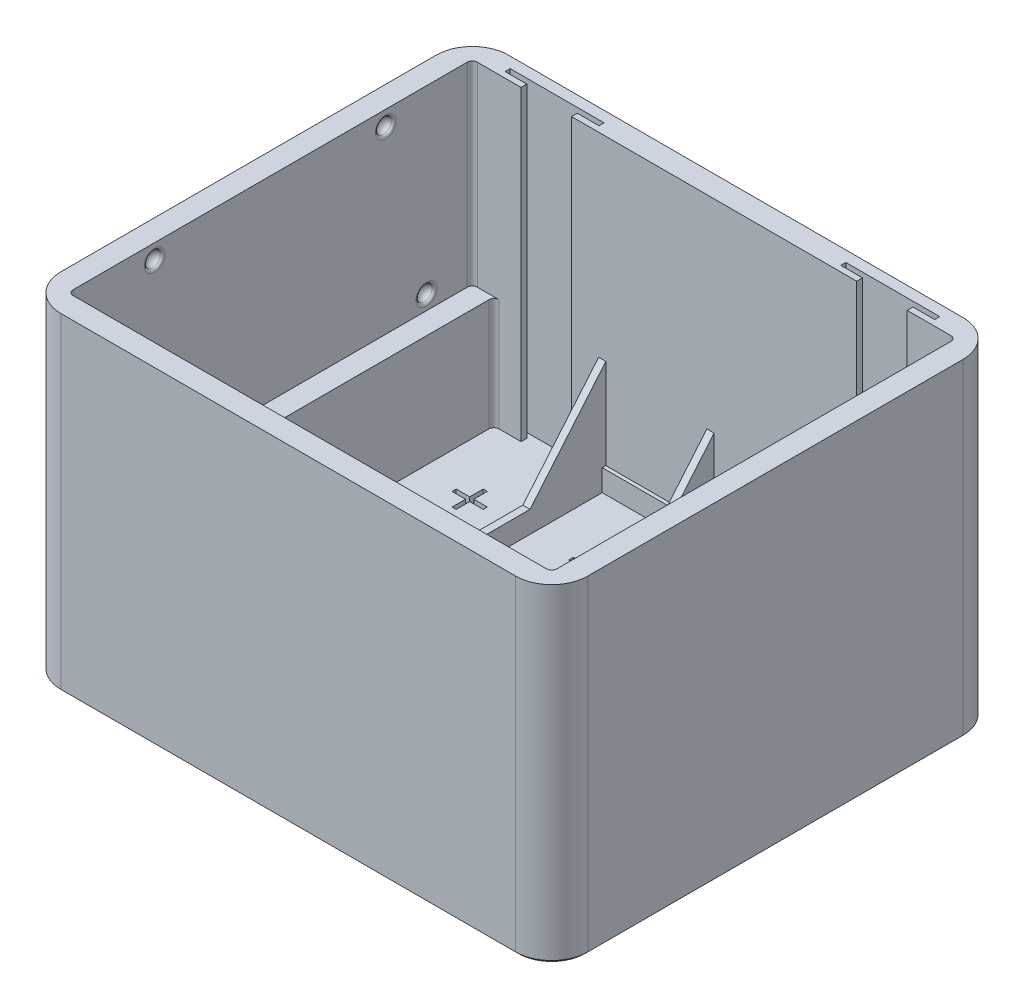
SolidWorks part; units mm, degrees
ref_plane "Front Plane" through (0, 0, 0) normal (0, 0, 1) x (1, 0, 0)
ref_plane "Top Plane" through (0, 0, 0) normal (0, 1, 0) x (1, 0, 0)
ref_plane "Right Plane" through (0, 0, 0) normal (1, 0, 0) x (0, 0, -1)
sketch "Sketch1" plane through (0, 0, 0) normal (0, 1, 0) x (1, 0, 0)
  line L1 (-33.5, -31) -> (33.5, -31)
  line L2 (-33.5, -31) -> (-33.5, 31)
  line L3 (-33.5, 31) -> (33.5, 31)
  line L4 (33.5, -31) -> (33.5, 31)
  line L5 (-33.5, -31) -> (33.5, 31) construction
  line L6 (-33.5, 31) -> (33.5, -31) construction
  point P0 (0, 0)
  dimension "D1" = 62
  dimension "D2" = 67
extrude "Boss-Extrude1" add sketch "Sketch1" along normal blind 3
sketch "Sketch2" plane through (0, 3, 0) normal (0, 1, 0) x (1, 0, 0)
  line L0 (-30.5, -28) -> (-30.5, 28)
  line L1 (-33.5, -31) -> (33.5, -31)
  line L2 (-33.5, -31) -> (-33.5, 31)
  line L3 (-33.5, 31) -> (33.5, 31)
  line L4 (33.5, -31) -> (33.5, 31)
  line L5 (-33.5, -31) -> (33.5, 31) construction
  line L6 (-33.5, 31) -> (33.5, -31) construction
  line L7 (-30.5, 28) -> (30.5, 28)
  line L8 (30.5, -28) -> (30.5, 28)
  line L9 (-30.5, -28) -> (30.5, -28)
  line L11 (-16, 28) -> (-15, 28)
  line L12 (-16, 28) -> (-16, -28)
  line L13 (-16, -28) -> (-15, -28)
  line L14 (-15, 28) -> (-15, -28)
  line L15 (-0.5, 28) -> (0.5, 28)
  line L16 (-0.5, 28) -> (-0.5, -28)
  line L17 (-0.5, -28) -> (0.5, -28)
  line L18 (0.5, 28) -> (0.5, -28)
  line L19 (15, 28) -> (16, 28)
  line L20 (15, 28) -> (15, -28)
  line L21 (15, -28) -> (16, -28)
  line L22 (16, 28) -> (16, -28)
  point P0 (0, 0)
  point P29 (0, 28)
  line M9 (33.5, -31) -> (33.5, 31)
  line M10 (33.5, 31) -> (-33.5, 31)
  line M11 (-33.5, 31) -> (-33.5, -31)
  line M12 (-33.5, -31) -> (33.5, -31)
  dimension "D2" = 14.5
  dimension "D3" = 14.5
  dimension "D4" = 14.5
  dimension "D1" = 3
extrude "Boss-Extrude2" add sketch "Sketch2" along normal blind 15.5 contours L9 L0 L7 L8 M12 M9 M10 M11 | L14 L7 L12 L9 | L18 L17 L16 L15 | L20 L21 L22 L19
sketch "Sketch4" plane through (-16, 0, 0) normal (-1, 0, 0) x (0, 0, 1)
  line L0 (-28, 18.5) -> (-17.5, 6)
  line L1 (-31, 18.5) -> (31, 18.5) construction
  line L2 (-17.5, 6) -> (17.5, 6)
  line L3 (17.5, 6) -> (28, 18.5)
  line L5 (-28, 3) -> (28, 3) construction
  line L6 (-28, 18.5) -> (28, 18.5)
  point P4 (0, 6)
  dimension "D1" = 35
  dimension "D2" = 3
extrude "Cut-Extrude1" cut sketch "Sketch4" against normal up to surface (32 mm away) up to face at (16, 10.75, 0)
sketch "Sketch5" plane through (-33.5, 0, 0) normal (-1, 0, 0) x (0, 0, 1)
  line L1 (-31, 18.5) -> (31, 18.5)
  line L2 (-31, 18.5) -> (-31, 0)
  line L3 (-31, 0) -> (31, 0)
  line L4 (31, 18.5) -> (31, 0)
extrude "Boss-Extrude4" add sketch "Sketch5" along normal blind 3
sketch "Sketch17" plane through (33.5, 0, 0) normal (1, 0, 0) x (0, 0, -1)
  line L1 (-31, 18.5) -> (31, 18.5)
  line L2 (-31, 18.5) -> (-31, 0)
  line L3 (-31, 0) -> (31, 0)
  line L4 (31, 18.5) -> (31, 0)
extrude "Boss-Extrude7" add sketch "Sketch17" along normal blind 3
sketch "Sketch7" plane through (0, 18.5, 0) normal (0, 1, 0) x (1, 0, 0)
  line L1 (-36.5, -31) -> (36.5, -31) construction
  line L3 (36.5, 31) -> (-36.5, 31) construction
  line L5 (-36.5, -31) -> (36.5, -31)
  line L6 (36.5, -31) -> (36.5, 31)
  line L7 (36.5, 31) -> (-36.5, 31)
  line L9 (33.5, 28) -> (-33.5, 28)
  line L10 (33.5, -28) -> (33.5, 28)
  line L11 (-33.5, -28) -> (33.5, -28)
  line L12 (-36.5, -31) -> (-36.5, 31)
  line L17 (-36.5, -31) -> (-36.5, 31) construction
  line L18 (-33.5, -28) -> (-33.5, 28)
  line L19 (-33.5, -28) -> (-33.5, 28) construction
  dimension "D1" = 3
extrude "Boss-Extrude5" add sketch "Sketch7" along normal blind 27
sketch "Sketch10" plane through (0, 3, 0) normal (0, 1, 0) x (1, 0, 0)
  text T0 "+" font "Century Gothic" height in points 24
  text T1 "-" font "Century Gothic" height in points 24
  text T2 "-" font "Century Gothic" height in points 24
  text T3 "+" font "Century Gothic" height in points 24
  text T4 "+" font "Century Gothic" height in points 24
  text T5 "-" font "Century Gothic" height in points 24
  text T6 "-" font "Century Gothic" height in points 24
  text T7 "+" font "Century Gothic" height in points 24
extrude "Cut-Extrude4" cut sketch "Sketch10" against normal blind 1
sketch "Sketch11" plane through (0, 18.5, 0) normal (0, 1, 0) x (1, 0, 0)
  line L1 (-16, -28) -> (-15, -28)
  line L2 (-16, -28) -> (-16, -27.5)
  line L3 (-16, -27.5) -> (-15, -27.5)
  line L4 (-15, -28) -> (-15, -27.5)
  line L5 (0.5, 28) -> (-0.5, 28)
  line L6 (0.5, 28) -> (0.5, 27.5)
  line L7 (0.5, 27.5) -> (-0.5, 27.5)
  line L8 (-0.5, 28) -> (-0.5, 27.5)
  line L9 (15, -27.5) -> (16, -27.5)
  line L10 (15, -27.5) -> (15, -28)
  line L11 (15, -28) -> (16, -28)
  line L12 (16, -27.5) -> (16, -28)
  line L14 (-15, -28) -> (-16, -28) construction
  line L15 (-16, 28) -> (-16, -28) construction
  line L16 (0.5, 28) -> (-0.5, 28) construction
  line L17 (-0.5, 17.5) -> (-0.5, 28) construction
  line L18 (16, -28) -> (15, -28) construction
  line L19 (15, -28) -> (15, -17.5) construction
  line L20 (-29.75, 28.8) -> (-26.75, 28.8)
  line L21 (-26.75, 28.8) -> (-26.75, 28)
  line L22 (-33.5, 28) -> (33.5, 28) construction
  line L23 (-26.75, 28) -> (-19.75, 28)
  line L24 (-19.75, 28) -> (-19.75, 28.8)
  line L25 (-19.75, 28.8) -> (-16.75, 28.8)
  line L26 (-16.75, 28.8) -> (-16.75, 29.5)
  line L27 (-16.75, 29.5) -> (-29.75, 29.5)
  line L28 (-29.75, 29.5) -> (-29.75, 28.8)
  line L29 (16.75, 28.8) -> (16.75, 29.5)
  line L30 (16.75, 29.5) -> (29.75, 29.5)
  line L31 (29.75, 29.5) -> (29.75, 28.8)
  line L32 (29.75, 28.8) -> (26.75, 28.8)
  line L33 (26.75, 28.8) -> (26.75, 28)
  line L34 (16, 28) -> (30.5, 28) construction
  line L35 (26.75, 28) -> (19.75, 28)
  line L36 (19.75, 28) -> (19.75, 28.8)
  line L37 (19.75, 28.8) -> (16.75, 28.8)
  line L38 (-30.5, 28) -> (-16, 28) construction
  line L39 (16, 28) -> (30.5, 28) construction
  point P15 (0, 28)
  point P17 (0, 28)
  point P21 (-15.5, -28)
  point P22 (-15.5, -28)
  point P30 (15.5, -28)
  point P31 (15.5, -28)
  point P42 (23.25, 28)
  point P51 (-23.25, 28)
  point P56 (-23.25, 28)
  point P57 (23.25, 28)
  dimension "D1" = 0.5
  dimension "D2" = 0.7
  dimension "D3" = 0.8
  dimension "D4" = 13
  dimension "D5" = 7
extrude "Cut-Extrude5" cut sketch "Sketch11" against normal up to surface (15.5 mm away) and the other way through all up to face at (-23.3935, 3, -17.5339)
fillet "Fillet1" radius 5 4 edges at (36.5, 22.75, 31) (-36.5, 22.75, 31) (-36.5, 22.75, -31) (36.5, 22.75, -31)
fillet "Fillet2" radius 0.7 8 edges at (30.5, 10.75, 28) (30.5, 10.75, -28) (-33.5, 32, -28) (-30.5, 10.75, -28) (-30.5, 10.75, 28) (-33.5, 32, 28) (33.5, 32, 28) (33.5, 32, -28)
chamfer "Chamfer2" distance 0.4 angle 45 8 edges at (0, 0, -31) (-35.0355, 0, -29.5355) (-36.5, 0, 0) (-35.0355, 0, 29.5355) (0, 0, 31) (35.0355, 0, -29.5355) (36.5, 0, 0) (35.0355, 0, 29.5355)
sketch "Sketch15" [suppressed] plane through (0, 0, -28) normal (0, 0, 1) x (1, 0, 0)
  line L0 (-15, 3) -> (-0.5, 3) construction
  line L2 (15, 3) -> (0.5, 3) construction
  line L3 (0.5, 3) -> (0.5, 17.9048) construction
  line L4 (0.5, 3) -> (0.5, 17.9048)
  line L5 (-0.5, 3) -> (-0.5, 17.9048) construction
  line L6 (-0.5, 3) -> (-0.5, 17.9048)
  line L7 (-7.75, 9.6425) -> (7.75, 9.6425)
  point P8 (-7.75, 3)
  point P10 (7.75, 3)
sketch "Sketch16" plane through (0, 3, 0) normal (0, 1, 0) x (1, 0, 0)
  line L6 (-15, 17.5) -> (-15, 28) construction
  line L7 (15, 28) -> (-15, 28)
  line L8 (15, 28) -> (15, 27.5)
  line L9 (15, 27.5) -> (-15, 27.5)
  line L10 (-15, 28) -> (-15, 27.5)
  line L11 (0.5, 27.5) -> (-0.5, 27.5) construction
extrude "Boss-Extrude6" add sketch "Sketch16" along normal blind 3
ref_plane "Plane1" through (0, 20.5, 0) normal (0, 1, 0) x (1, 0, 0)
sketch "Sketch19" plane through (0, 20.5, 0) normal (0, 1, 0) x (1, 0, 0)
  line L0 (33.5, -27.3) -> (33.5, 27.3) construction
  line L1 (33.5, -27.3) -> (33.5, 27.3) construction
  line L2 (33.5, -20.55) -> (33.5, -21.65)
  line L3 (33.5, -21.65) -> (34.6, -21.65)
  line L4 (29.8, -28) -> (32.8, -28) construction
  arc A0 (33.5, -20.55) -> (34.6, -21.65) centre (33.5, -21.65) cw
  dimension "D1" = 1.1
  dimension "D2" = 6.35
revolve "Cut-Revolve1" cut sketch "Sketch19" angle 360 about L3
mirror "Mirror1" about plane through (0, 0, 0) normal (0, 0, 1) of "Cut-Revolve1"
mirror "Mirror2" about plane through (0, 0, 0) normal (1, 0, 0) of "Mirror1", "Cut-Revolve1"
fillet "Fillet3" radius 0.4 4 edges at (33.5, 20.5, 22.75) (33.5, 20.5, -22.75) (-33.5, 20.5, 22.75) (-33.5, 20.5, -22.75)
ref_plane "Plane2" through (0, 43.4, 0) normal (0, 1, 0) x (1, 0, 0)
sketch "Sketch20" plane through (0, 43.4, 0) normal (0, 1, 0) x (1, 0, 0)
  line L0 (-33.5, 16) -> (-34.6, 16)
  line L1 (-33.5, 27.3) -> (-33.5, -27.3) construction
  line L2 (-33.5, 17.1) -> (-33.5, 16)
  line L3 (-33.5, 16) -> (-33.5, -16) construction
  arc A0 (-34.6, 16) -> (-33.5, 17.1) centre (-33.5, 16) cw
  point P6 (-33.5, 0)
  point P12 (-33.5, 17.5726)
  point P13 (0, 0)
  dimension "D1" = 1.1
  dimension "D2" = 32
revolve "Cut-Revolve2" cut sketch "Sketch20" angle 360 about L0
mirror "Mirror3" about plane through (0, 0, 0) normal (0, 0, 1) of "Cut-Revolve2"
mirror "Mirror4" about plane through (0, 0, 0) normal (1, 0, 0) of "Mirror3", "Cut-Revolve2"
fillet "Fillet4" radius 0.4 4 edges at (33.5, 43.4, 17.1) (33.5, 43.4, -17.1) (-33.5, 43.4, 17.1) (-33.5, 43.4, -17.1)
